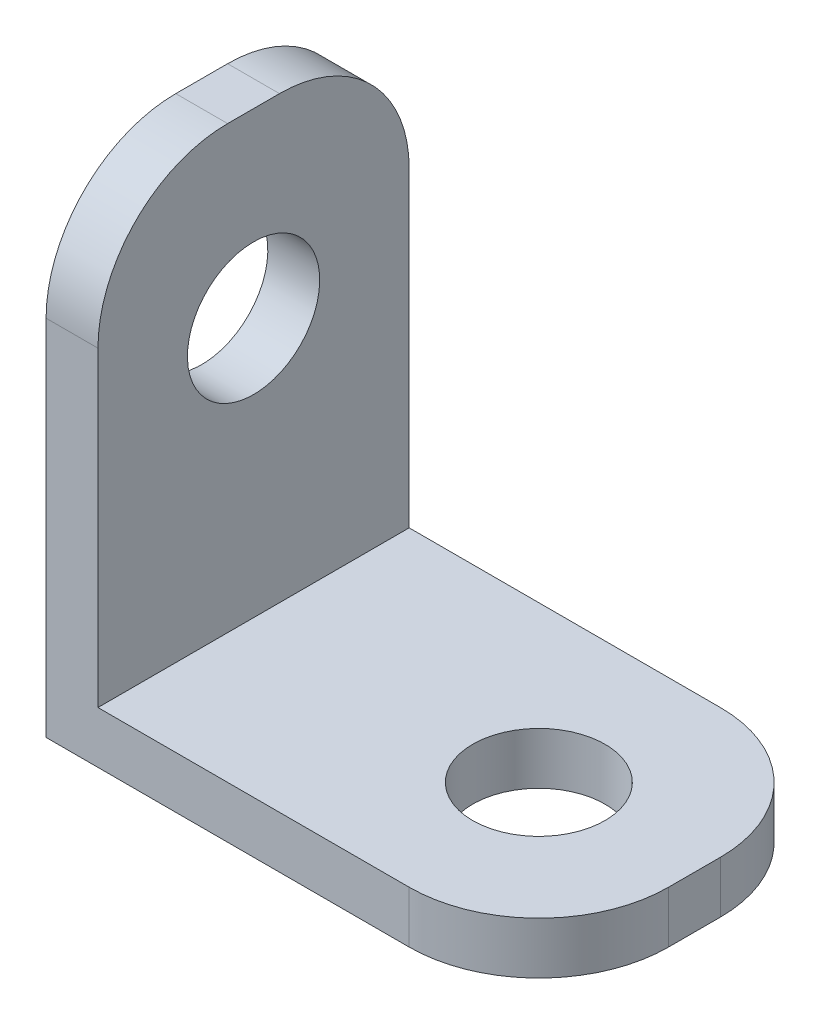
SolidWorks part; units mm, degrees
material "1023 Листовая углеродистая сталь (SS)"
ref_plane "Спереди" through (0, 0, 0) normal (0, 0, 1) x (1, 0, 0)
ref_plane "Сверху" through (0, 0, 0) normal (0, 1, 0) x (1, 0, 0)
ref_plane "Справа" through (0, 0, 0) normal (1, 0, 0) x (0, 0, -1)
sketch "Эскиз1" plane through (0, 0, 0) normal (0, 0, 1) x (1, 0, 0)
  line L0 (0, 0) -> (0, 19)
  line L1 (0, 19) -> (2, 19)
  line L2 (2, 19) -> (2, 2)
  line L3 (2, 2) -> (19, 2)
  line L4 (19, 2) -> (19, 0)
  line L5 (19, 0) -> (0, 0)
  point P3 (1, 19)
  point P8 (19, 1)
  dimension "D1" = 2
  dimension "D2" = 2
  dimension "D3" = 19
  dimension "D4" = 19
extrude "Бобышка-Вытянуть1" add sketch "Эскиз1" along normal blind 12
sketch "Эскиз2" plane through (2, 0, 0) normal (1, 0, 0) x (0, 0, -1)
  line L0 (-12, 2) -> (-12, 19) construction
  line L1 (-6, 0) -> (-6, 19.5429) construction
  line L2 (-12, 0) -> (0, 0) construction
  line L3 (-12, 19) -> (0, 19) construction
  line L4 (-12, 14) -> (-12, 19)
  line L5 (-12, 19) -> (-7, 19)
  line L6 (0, 14) -> (0, 19)
  line L7 (0, 19) -> (-5, 19)
  line L8 (-12, 2) -> (0, 2) construction
  arc A0 (-12, 14) -> (-7, 19) centre (-7, 14) cw
  arc A1 (0, 14) -> (-5, 19) centre (-5, 14) ccw
  circle A2 centre (-6, 12) radius 2.55
  point P0 (-7, 14)
  dimension "D3" = 5
  dimension "D4" = 10
  dimension "D5" = 5.1
  dimension "D1" = 5
  dimension "D2" = 5
extrude "Вырез-Вытянуть1" cut sketch "Эскиз2" against normal through all
sketch "Эскиз3" plane through (0, 2, 0) normal (0, 1, 0) x (1, 0, 0)
  line L0 (19, 0) -> (2, 0) construction
  line L2 (19, -12) -> (19, 0) construction
  line L3 (14, 0) -> (19, 0)
  line L4 (19, 0) -> (19, -5)
  line L5 (21.7926, -6) -> (-0.9534, -6) construction
  line L6 (2, -7) -> (2, -5) construction
  line L7 (14, -12) -> (19, -12)
  line L8 (19, -12) -> (19, -7)
  arc A0 (14, 0) -> (19, -5) centre (14, -5) cw
  circle A1 centre (13, -6) radius 2.55
  arc A2 (14, -12) -> (19, -7) centre (14, -7) ccw
  point P0 (14, -5)
  dimension "D3" = 5.1
  dimension "D1" = 5
  dimension "D2" = 5
  dimension "D4" = 11
extrude "Вырез-Вытянуть2" cut sketch "Эскиз3" against normal through all
equation "\"D2@Эскиз1\"=\"D1@Эскиз1\""
equation "\"D4@Эскиз1\"=\"D3@Эскиз1\""
